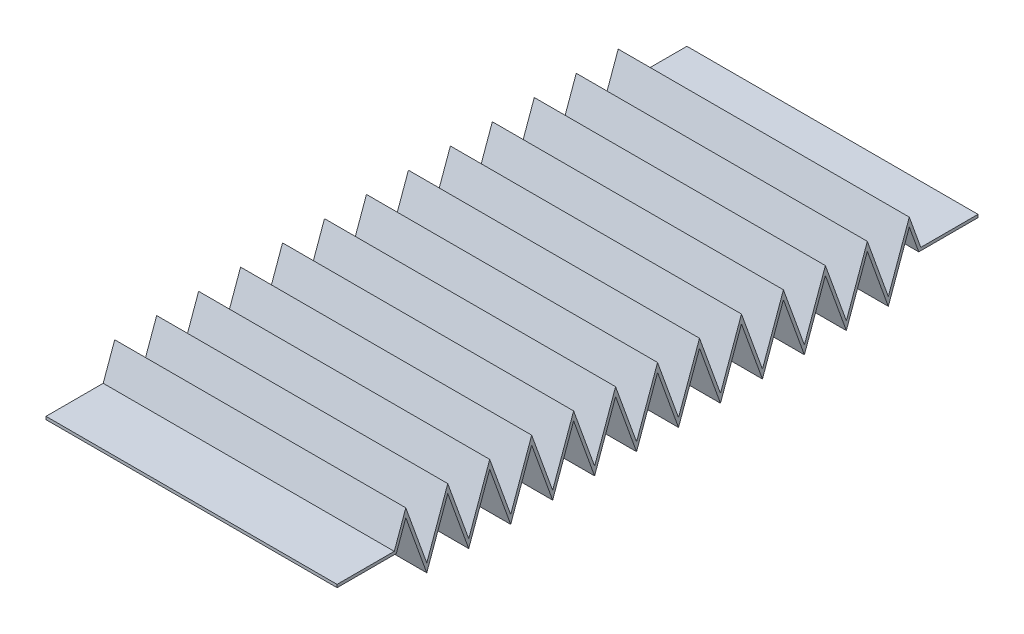
SolidWorks part; units mm, degrees
ref_plane "Front Plane" through (0, 0, 0) normal (0, 0, 1) x (1, 0, 0)
ref_plane "Top Plane" through (0, 0, 0) normal (0, 1, 0) x (1, 0, 0)
ref_plane "Right Plane" through (0, 0, 0) normal (1, 0, 0) x (0, 0, -1)
sketch "Sketch2" plane through (0, 0, 0) normal (0, 0, 1) x (1, 0, 0)
  line L1 (-27.5, 10) -> (27.5, 10)
  line L2 (-27.5, 10) -> (-27.5, 0)
  line L3 (-27.5, 0) -> (27.5, 0)
  line L4 (27.5, 10) -> (27.5, 0)
  point P4 (0, 0)
  dimension "D1" = 10
  dimension "D2" = 55
sketch "Sketch3" plane through (0, 0, 0) normal (1, 0, 0) x (0, 0, -1)
  line L0 (0, 10) -> (110.0919, 10) construction
  line L1 (0, 0) -> (110.0919, 0) construction
  line L3 (10, 5) -> (11.8018, 10)
  line L4 (11.8018, 10) -> (15.4055, 0)
  line L5 (15.4055, 0) -> (19.0092, 10)
  line L6 (19.0092, 10) -> (22.6129, 0)
  line L7 (22.6129, 0) -> (26.2165, 10)
  line L8 (26.2165, 10) -> (29.8202, 0)
  line L9 (29.8202, 0) -> (33.4239, 10)
  line L10 (33.4239, 10) -> (37.0276, 0)
  line L11 (37.0276, 0) -> (40.6312, 10)
  line L12 (40.6312, 10) -> (44.2349, 0)
  line L13 (44.2349, 0) -> (47.8386, 10)
  line L14 (47.8386, 10) -> (51.4423, 0)
  line L15 (51.4423, 0) -> (55.0459, 10)
  line L16 (55.0459, 10) -> (58.6496, 0)
  line L17 (58.6496, 0) -> (62.2533, 10)
  line L18 (62.2533, 10) -> (65.857, 0)
  line L19 (0, 10) -> (0, 0) construction
  line L20 (65.857, 0) -> (69.4606, 10)
  line L21 (69.4606, 10) -> (73.0643, 0)
  line L22 (73.0643, 0) -> (76.668, 10)
  line L23 (76.668, 10) -> (80.2717, 0)
  line L24 (80.2717, 0) -> (83.8753, 10)
  line L25 (83.8753, 10) -> (87.479, 0)
  line L26 (87.479, 0) -> (91.0827, 10)
  line L27 (91.0827, 10) -> (94.6864, 0)
  line L28 (94.6864, 0) -> (98.29, 10)
  line L29 (98.29, 10) -> (100.0919, 5)
  line L30 (110.0919, 10) -> (110.0919, 0) construction
  line L31 (10, 5) -> (0, 5)
  line L32 (100.0919, 5) -> (110.0919, 5)
  line L33 (110.0919, -12.3958) -> (110.0919, -19.8536) construction
  dimension "D2" = 10
  dimension "D1" = 10
  dimension "D3" = 10
extrude "Extrude-Thin1" add sketch "Sketch3" against normal mid plane 50 thin thin type mid plane wall 0.5
